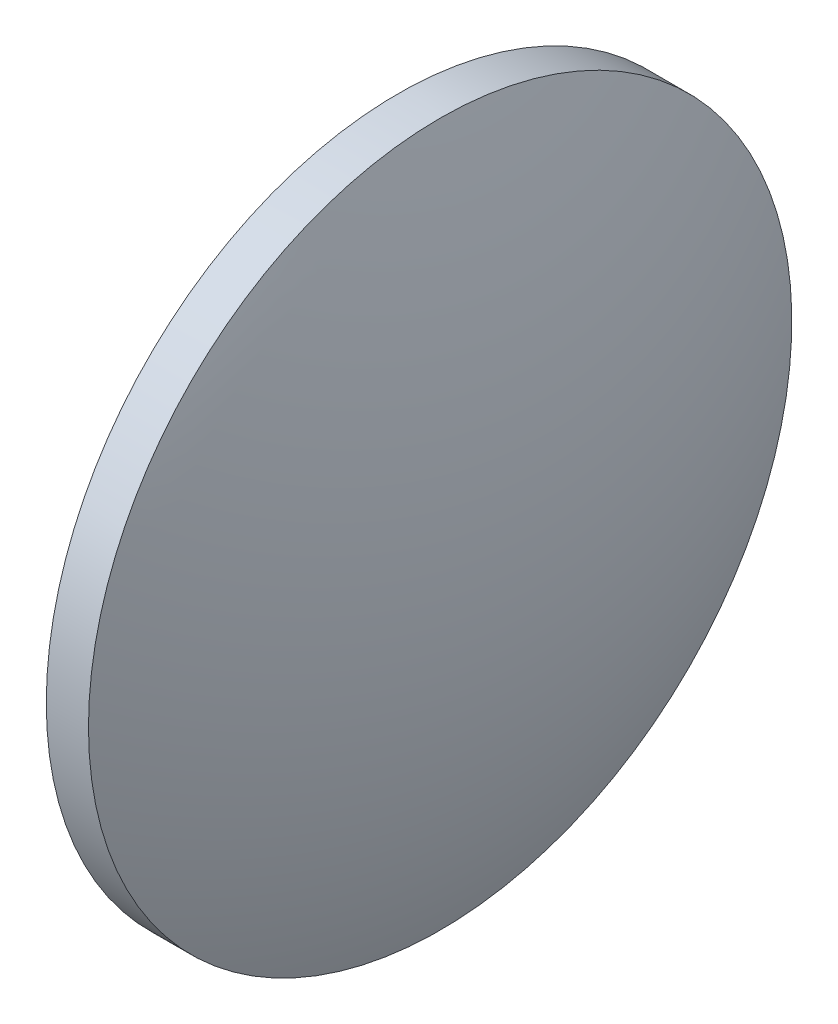
SolidWorks part; units mm, degrees
ref_plane "前视基准面" through (0, 0, 0) normal (0, 0, 1) x (1, 0, 0)
ref_plane "上视基准面" through (0, 0, 0) normal (0, 1, 0) x (1, 0, 0)
ref_plane "右视基准面" through (0, 0, 0) normal (1, 0, 0) x (0, 0, -1)
sketch "草图1" plane through (0, 0, 0) normal (0, 0, 1) x (1, 0, 0)
  line L0 (547.6337, 7.5746) -> (563.6907, 7.5746) construction
  line L1 (549.6628, 7.5746) -> (549.6628, 20.0746)
  line L2 (553.6628, 7.5746) -> (549.6628, 7.5746)
  line L5 (549.6628, 20.0746) -> (551.1628, 20.0746)
  arc A0 (553.6628, 7.5746) -> (551.1628, 20.0746) centre (521.1628, 7.5746) ccw
revolve "旋转1" add sketch "草图1" angle 360 about L0
